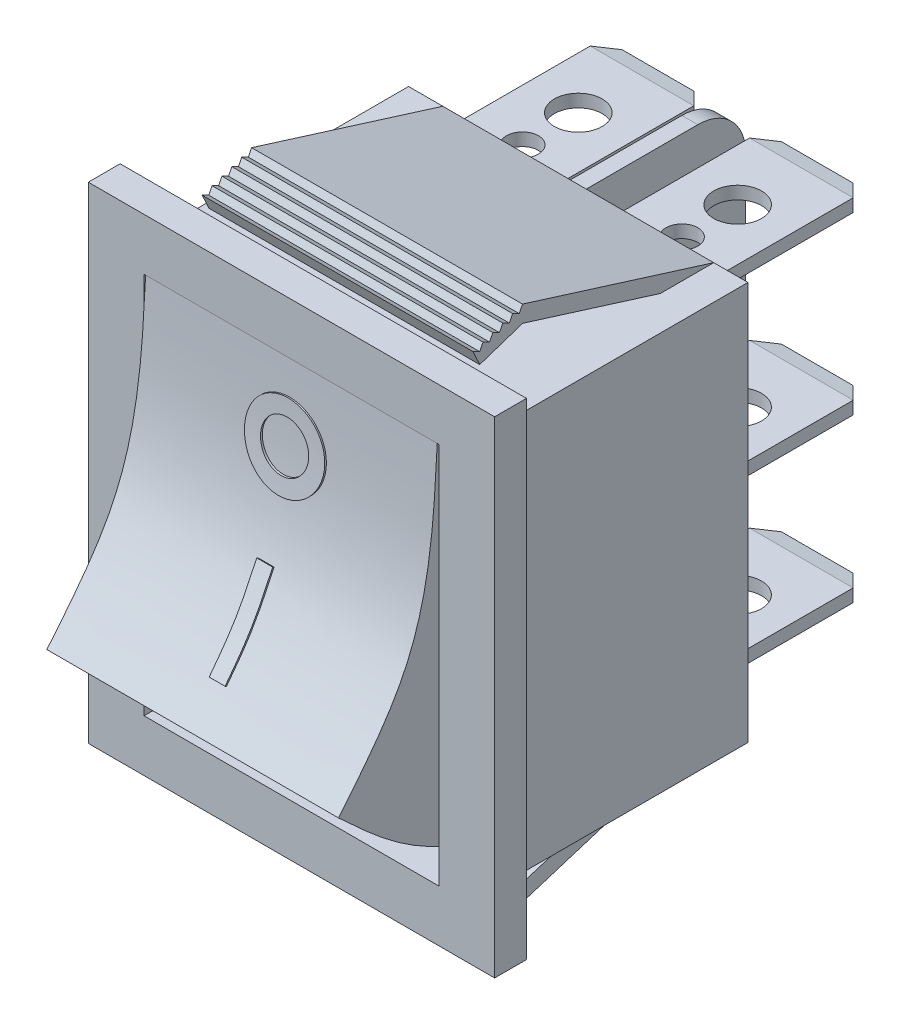
SolidWorks part; units mm, degrees
ref_plane "前视基准面" through (0, 0, 0) normal (0, 0, 1) x (1, 0, 0)
ref_plane "上视基准面" through (0, 0, 0) normal (0, 1, 0) x (1, 0, 0)
ref_plane "右视基准面" through (0, 0, 0) normal (1, 0, 0) x (0, 0, -1)
sketch "草图1" plane through (0, 0, 0) normal (0, 0, 1) x (1, 0, 0)
  line L1 (-12.75, -15.25) -> (12.75, -15.25)
  line L2 (-12.75, -15.25) -> (-12.75, 15.25)
  line L3 (-12.75, 15.25) -> (12.75, 15.25)
  line L4 (12.75, -15.25) -> (12.75, 15.25)
  line L5 (-12.75, -15.25) -> (12.75, 15.25) construction
  line L6 (-12.75, 15.25) -> (12.75, -15.25) construction
  point P0 (0, 0)
  dimension "D1" = 30.5
  dimension "D2" = 25.5
extrude "拉伸1" add sketch "草图1" against normal blind 2
sketch "草图2" plane through (0, 0, -2) normal (0, 0, -1) x (-1, 0, 0)
  line L1 (-10.65, -12.5) -> (10.65, -12.5)
  line L2 (-10.65, -12.5) -> (-10.65, 12.5)
  line L3 (-10.65, 12.5) -> (10.65, 12.5)
  line L4 (10.65, -12.5) -> (10.65, 12.5)
  line L5 (-10.65, -12.5) -> (10.65, 12.5) construction
  line L6 (-10.65, 12.5) -> (10.65, -12.5) construction
  point P0 (0, 0)
  dimension "D1" = 25
  dimension "D2" = 21.3
extrude "拉伸2" add sketch "草图2" along normal blind 16
sketch "草图3" plane through (0, 0, -18) normal (0, 0, -1) x (-1, 0, 0)
  line L0 (10.65, 12.5) -> (-10.65, 12.5) construction
  line L1 (-0.5, -12.5) -> (0.5, -12.5)
  line L2 (-0.5, -12.5) -> (-0.5, 12.5)
  line L3 (-0.5, 12.5) -> (0.5, 12.5)
  line L4 (0.5, -12.5) -> (0.5, 12.5)
  line L5 (-0.5, -12.5) -> (0.5, 12.5) construction
  line L6 (-0.5, 12.5) -> (0.5, -12.5) construction
  line L7 (1.75, -0.4) -> (1.75, 0.4)
  line L8 (1.75, 10.6) -> (1.75, 11.4)
  line L9 (1.75, 10.6) -> (8.25, 10.6)
  line L10 (8.25, 10.6) -> (8.25, 11.4)
  line L11 (8.25, -0.4) -> (8.25, 0.4)
  line L12 (1.75, 11.4) -> (8.25, 11.4)
  line L13 (1.75, -9.8) -> (8.25, -9.8)
  line L14 (1.75, 0.4) -> (8.25, 0.4)
  line L15 (1.75, -0.4) -> (8.25, -0.4)
  line L16 (8.25, -10.6) -> (8.25, -9.8)
  line L17 (1.75, -10.6) -> (8.25, -10.6)
  line L18 (1.75, -10.6) -> (1.75, -9.8)
  line L19 (0, 12.5) -> (0, -12.5) construction
  point P0 (0, 0)
  point P8 (0, 0)
  dimension "D1" = 1
  dimension "D2" = 11
  dimension "D3" = 0.8
  dimension "D5" = 11
  dimension "D4" = 6.5
extrude "拉伸3" add sketch "草图3" along normal blind 10
fillet "圆角1" radius 3 2 edges at (0, -12.5, -28) (0, 12.5, -28)
chamfer "倒角3" distance 1 distance2 0.2 6 edges at (-5, 11.4, -28) (-5, 10.6, -28) (-5, -9.8, -28) (-5, -10.6, -28) (-5, 0.4, -28) (-5, -0.4, -28)
chamfer "倒角4" distance 1 angle 45 6 edges at (-8.25, -10.2, -28) (-1.75, -10.2, -28) (-1.75, 0, -28) (-8.25, 0, -28) (-8.25, 11, -28) (-1.75, 11, -28)
sketch "草图4" plane through (0, 11.4, 0) normal (0, 1, 0) x (-1, 0, 0)
  line L0 (7.25, -28) -> (2.75, -28) construction
  circle A0 centre (5, -23) radius 1.5
  circle A1 centre (5, -19.5) radius 1
  dimension "D1" = 3
  dimension "D4" = 2
  dimension "D2" = 5
  dimension "D3" = 8.5
extrude "拉伸4" cut sketch "草图4" against normal through all
mirror "镜向4" about plane through (0, 0, 0) normal (1, 0, 0) of bodies 117
sketch "草图5" plane through (0, 0, 0) normal (0, 0, 1) x (1, 0, 0)
  line L1 (-9.25, -12) -> (9.25, -12)
  line L2 (-9.25, -12) -> (-9.25, 12)
  line L3 (-9.25, 12) -> (9.25, 12)
  line L4 (9.25, -12) -> (9.25, 12)
  line L5 (-9.25, -12) -> (9.25, 12) construction
  line L6 (-9.25, 12) -> (9.25, -12) construction
  point P0 (0, 0)
  dimension "D1" = 24
  dimension "D2" = 18.5
extrude "拉伸5" cut sketch "草图5" against normal blind 5
sketch "草图6" plane through (0, 0, 0) normal (1, 0, 0) x (0, 0, -1)
  line L4 (0, 12) -> (5, 12)
  line L7 (5, 12) -> (5, -12)
  spline S0 degree 3 poles (5, -12) (2.5598, -11.088) (-1.6116, -9.529) (-4.8543, -6.505) (-6.2, -5.25) knots 0 0 0 0 0.585001 1 1 1 1
  spline S1 degree 3 poles (0, 12) (-0.2099, 8.0687) (-0.5549, 1.6059) (-4.6112, -3.3204) (-6.2, -5.25) knots 0 0 0 0 0.608305 1 1 1 1
extrude "拉伸6" add sketch "草图6" along normal blind 9.15 and the other way blind 9.15
sketch "草图7" plane through (0, 0, 0) normal (1, 0, 0) x (0, 0, -1)
  line L0 (-1.6773, 1.7927) -> (-1.5869, 1.75)
  line L1 (-4.6635, -3.1891) -> (-4.5842, -3.25)
  spline S0 degree 3 poles (-4.5842, -3.25) (-4.1197, -2.6453) (-2.9302, -1.0969) (-2.0956, 0.6719) (-1.5869, 1.75) knots 0 0 0 0 0.39051 1 1 1 1
  spline S1 degree 3 poles (0, 12) (-0.2099, 8.0687) (-0.5549, 1.6059) (-4.6112, -3.3204) (-6.2, -5.25) knots 0 0 0 0 0.608305 1 1 1 1 construction
  spline S2 degree 1 poles (-4.6635, -3.1891) (-1.6773, 1.7927) knots 0 0 1 1 construction
  spline S3 degree 3 poles (-4.6635, -3.1891) (-4.0734, -2.4209) (-2.9131, -0.8615) (-2.0922, 0.9135) (-1.6773, 1.7927) knots 0 0 0 0 0.5 1 1 1 1
  dimension "D3" = 0.1
extrude "拉伸8" add sketch "草图7" along normal blind 0.5 and the other way blind 0.5 separate body
sketch "草图8" plane through (0, 0, 0) normal (0, 0, 1) x (1, 0, 0)
  line L0 (-9.15, 12) -> (9.15, 12) construction
  circle A0 centre (0, 7.5) radius 2.5
  circle A1 centre (0, 7.5) radius 1.5
  dimension "D1" = 4.5
  dimension "D2" = 5
  dimension "D3" = 3
extrude "拉伸9" add sketch "草图8" along normal blind 1.5
sketch "草图9" plane through (0, 0, 0) normal (1, 0, 0) x (0, 0, -1)
  line L0 (-0.0999, 12.0046) -> (-2.228, 12.0046)
  line L1 (-2.228, 12.0046) -> (-2.228, 4.2649)
  line L2 (-2.228, 4.2649) -> (-0.9382, 4.2649)
  spline S3 degree 3 poles (-0.0999, 12.0046) (-0.1593, 10.7071) (-0.2753, 8.1076) (-0.7164, 5.5443) (-0.9382, 4.2649) knots 0 0 0 0 0.5 1 1 1 1
extrude "拉伸10" cut sketch "草图9" against normal through all and the other way through all
sketch "草图10" plane through (0, 0, 0) normal (1, 0, 0) x (0, 0, -1)
  line L0 (29.6963, 0) -> (0, 0) construction
  line L1 (0, -15.25) -> (0, 15.25) construction
  line L2 (6, 16.25) -> (5.7933, 15.8365)
  line L3 (18, 12.5) -> (2, 12.5) construction
  line L4 (18, 12.5) -> (6, 16.25)
  line L5 (5.7933, 15.8365) -> (5.3798, 16.0433)
  line L6 (5.3798, 16.0433) -> (5.1731, 15.6298)
  line L7 (5.1731, 15.6298) -> (4.7596, 15.8365)
  line L8 (2.8991, 15.2164) -> (3.3162, 14.3013)
  line L9 (3.9327, 15.2164) -> (3.5193, 15.4231)
  line L10 (4.5529, 15.4231) -> (4.1395, 15.6298)
  line L11 (4.1395, 15.6298) -> (3.9327, 15.2164)
  line L12 (4.7596, 15.8365) -> (4.5529, 15.4231)
  line L13 (3.3125, 15.0096) -> (2.8991, 15.2164)
  line L14 (3.5193, 15.4231) -> (3.3125, 15.0096)
  line L15 (14.6474, 12.5) -> (6.0099, 15.1992)
  line L16 (6.0099, 15.1992) -> (3.3162, 14.3013)
  line L17 (17.7017, 11.5455) -> (6.5139, 15.0417) construction
  line L18 (14.6474, 12.5) -> (18, 12.5)
  line L31 (6.2405, 14.4949) -> (4.9326, 15.1488) construction
  line L34 (6.5139, 15.0417) -> (6.2405, 14.4949) construction
  dimension "D2" = 17.354
  dimension "D4" = 90
  dimension "D5" = 1
extrude "拉伸11" add sketch "草图10" along normal blind 8.5 and the other way blind 8.5
mirror "镜向5" about plane through (0, 0, 0) normal (0, 1, 0) of "拉伸11"
ref_plane "基准面1" through (-10.25, 0, 0) normal (-1, 0, 0) x (0, 0, 1)
sketch "草图11" plane through (-10.25, 0, 0) normal (-1, 0, 0) x (0, 0, 1)
  line L0 (0, 0) -> (-18, 0) construction
  line L1 (0, 15.25) -> (0, -15.25) construction
  line L2 (-18, -12.5) -> (-18, 12.5) construction
  line L3 (-2, 13.7) -> (-3, 13.7)
  line L5 (-2, 12.5) -> (-2, 13.7)
  line L6 (-4, 15.25) -> (-4, -15.25)
  line L7 (-4, 12.7) -> (-4, 12.5)
  line L8 (-2, 12.5) -> (-4, 12.5)
  line L9 (-18, 12.5) -> (-2, 12.5) construction
  line L10 (-2, 15.25) -> (-2, -15.25) construction
  line L11 (0, 13.7) -> (-18, 13.7) construction
  line L13 (-2, -12.5) -> (-4, -12.5)
  line L14 (-4, -12.7) -> (-4, -12.5)
  line L15 (-2, -12.5) -> (-2, -13.7)
  line L16 (-2, -13.7) -> (-3, -13.7)
  arc A0 (-4, 12.7) -> (-3, 13.7) centre (-3, 12.7) cw
  arc A1 (-4, -12.7) -> (-3, -13.7) centre (-3, -12.7) ccw
  dimension "D3" = 1
  dimension "D1" = 13.7
  dimension "D2" = 2
extrude "拉伸12" add sketch "草图11" against normal blind 1.5
sketch "草图12" plane through (0, 0, -2) normal (0, 0, -1) x (-1, 0, 0)
  line L1 (-10.75, -14.5) -> (10.75, -14.5)
  line L2 (-10.75, -14.5) -> (-10.75, 14.5)
  line L3 (-10.75, 14.5) -> (10.75, 14.5)
  line L4 (10.75, -14.5) -> (10.75, 14.5)
  line L5 (-10.75, -14.5) -> (10.75, 14.5) construction
  line L6 (-10.75, 14.5) -> (10.75, -14.5) construction
  point P0 (0, 0)
  dimension "D1" = 21.5
  dimension "D2" = 29
